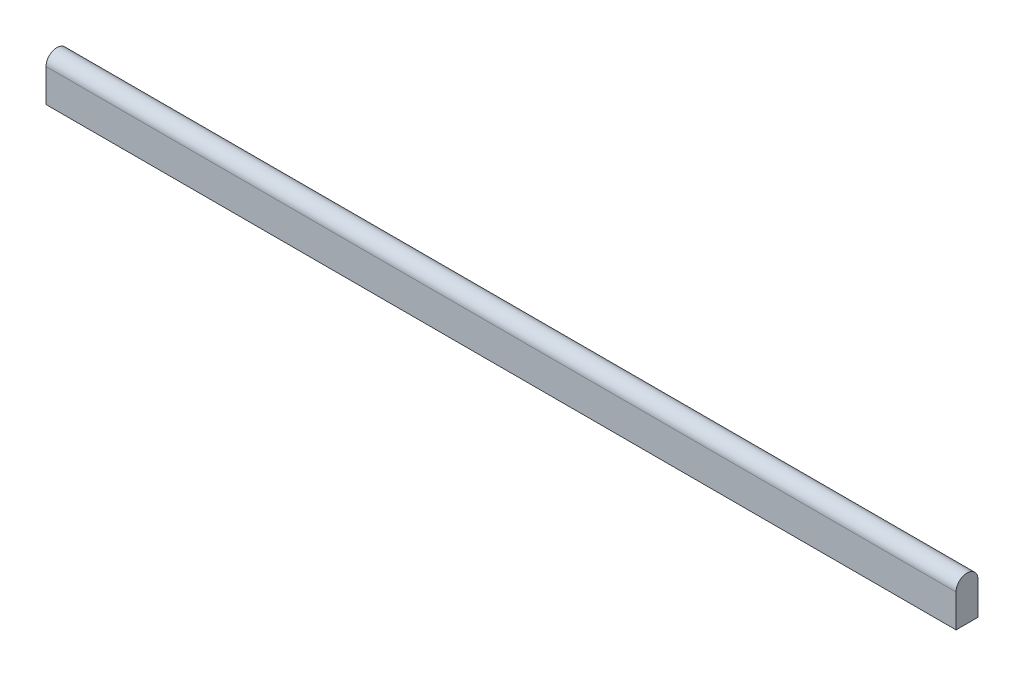
SolidWorks part; units mm, degrees
ref_plane "Plan de face" through (0, 0, 0) normal (0, 0, 1) x (1, 0, 0)
ref_plane "Plan de dessus" through (0, 0, 0) normal (0, 1, 0) x (1, 0, 0)
ref_plane "Plan de droite" through (0, 0, 0) normal (1, 0, 0) x (0, 0, -1)
sketch "Esquisse1" plane through (0, 0, 0) normal (1, 0, 0) x (0, 0, -1)
  line L0 (-2, 0) -> (-2, -6)
  line L1 (-2, -6) -> (2, -6)
  line L2 (2, -6) -> (2, 0)
  arc A0 (-2, 0) -> (2, 0) centre (0, 0) cw
  dimension "D1" = 2
  dimension "D2" = 6
extrude "Extrusion1" add sketch "Esquisse1" along normal blind 166
